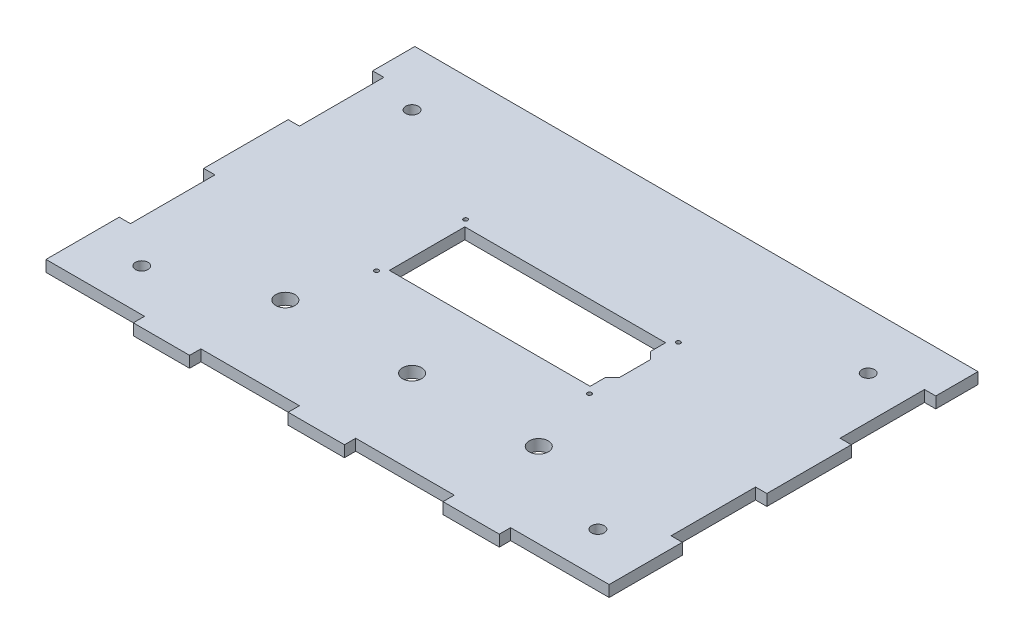
SolidWorks part; units mm, degrees
ref_plane "Plano frontal" through (0, 0, 0) normal (0, 0, 1) x (1, 0, 0)
ref_plane "Plano superior" through (0, 0, 0) normal (0, 1, 0) x (1, 0, 0)
ref_plane "Plano direito" through (0, 0, 0) normal (1, 0, 0) x (0, 0, -1)
sketch "Esboço1" plane through (0, 0, 0) normal (0, 1, 0) x (1, 0, 0)
  line L0 (-100, 75) -> (100, -75) construction
  line L1 (-100, 75) -> (100, 75)
  line L2 (-100, 75) -> (-100, -75)
  line L3 (-100, -75) -> (100, -75)
  line L4 (100, 75) -> (100, -75)
  line L5 (0, 75) -> (0, -75) construction
  line L6 (-100, 0) -> (100, 0) construction
  line L7 (-35.65, -13.4) -> (35.65, -13.4)
  line L8 (-35.65, 13.4) -> (35.65, 13.4)
  line L9 (-35.65, 13.4) -> (-35.65, -13.4)
  line L10 (35.65, 13.4) -> (35.65, 8)
  line L11 (35.65, -13.4) -> (35.65, -8)
  line L12 (35.65, 8) -> (38.15, 5.5)
  line L13 (38.15, 5.5) -> (38.15, -5.5)
  line L14 (38.15, -5.5) -> (35.65, -8)
  circle A0 centre (-37.8, 15.8) radius 0.75
  circle A1 centre (37.8, 15.8) radius 0.75
  circle A2 centre (37.8, -15.8) radius 0.75
  circle A3 centre (-37.8, -15.8) radius 0.75
  point P4 (0, 0)
  point P12 (0, -13.4)
  point P14 (0, 13.4)
  dimension "D3" = 1.5
  dimension "D4" = 37.8
  dimension "D1" = 200
  dimension "D2" = 150
  dimension "D5" = 15.8
  dimension "D8" = 31.6
  dimension "D9" = 75.6
  dimension "D10" = 71.3
  dimension "D11" = 26.8
  dimension "D12" = 13.4
  dimension "D13" = 5.4
  dimension "D14" = 5.4
  dimension "D15" = 2.5
  dimension "D16" = 135
  dimension "D17" = 11
  dimension "D6" = 2
  dimension "D7" = 2
extrude "Ressalto-extrusão1" add sketch "Esboço1" along normal blind 4
sketch "Esboço2" plane through (0, 4, 0) normal (0, 1, 0) x (1, 0, 0)
  line L0 (-65, -75) -> (-65, -71)
  line L1 (-100, -75) -> (100, -75) construction
  line L2 (-65, -71) -> (-45, -71)
  line L3 (-45, -71) -> (-45, -75)
  line L4 (-45, -75) -> (-10, -75)
  line L5 (-10, -75) -> (-10, -71)
  line L6 (-10, -71) -> (10, -71)
  line L7 (10, -71) -> (10, -75)
  line L8 (10, -75) -> (45, -75)
  line L9 (45, -75) -> (45, -71)
  line L10 (45, -71) -> (65, -71)
  line L11 (65, -71) -> (65, -75)
  line L12 (-100, 75) -> (-100, -75) construction
  line L13 (0, 0) -> (0, 75) construction
  line L15 (10, -71) -> (45, -71)
  line L17 (-65, -75) -> (-100, -75)
  line L18 (-100, -75) -> (-100, -71)
  line L19 (-100, -71) -> (-65, -71)
  line L20 (-45, -71) -> (-10, -71)
  line L21 (65, -71) -> (100, -71)
  line L22 (100, -75) -> (100, 75) construction
  line L23 (100, -45) -> (96, -45)
  line L24 (96, -45) -> (96, -15)
  line L25 (96, -15) -> (100, -15)
  line L26 (100, -15) -> (100, 15)
  line L27 (100, 15) -> (96, 15)
  line L28 (96, 15) -> (96, 45)
  line L29 (96, 45) -> (100, 45)
  line L30 (100, 75) -> (-100, 75) construction
  line L31 (-100, -15) -> (-100, -45)
  line L32 (-100, 45) -> (-100, 15)
  line L33 (-96, 45) -> (-100, 45)
  line L34 (100, 45) -> (100, 15)
  line L35 (100, -15) -> (100, -45)
  line L36 (-96, 15) -> (-96, 45)
  line L37 (-100, 15) -> (-96, 15)
  line L38 (-100, -15) -> (-100, 15)
  line L39 (-96, -15) -> (-100, -15)
  line L40 (-96, -45) -> (-96, -15)
  line L41 (-100, -45) -> (-96, -45)
  line M8 (-100, 75) -> (-100, -75)
  line M9 (-100, -75) -> (100, -75)
  line M10 (100, -75) -> (100, 75)
  dimension "D1" = 35
  dimension "D2" = 35
  dimension "D3" = 35
  dimension "D4" = 20
  dimension "D5" = 20
  dimension "D6" = 20
  dimension "D7" = 4
  dimension "D8" = 30
  dimension "D9" = 30
  dimension "D10" = 30
  dimension "D11" = 30
  dimension "D12" = 4
extrude "Corte-extrusão1" cut sketch "Esboço2" against normal through all contours L20 L3 L5 M9 | L15 L7 L9 M9 | L21 L11 M9 M10 | L19 L0 M8 M9 | L27 L28 L29 L34 | L35 L23 L24 L25 | L37 L36 L33 L32 | L31 L41 L40 L39
sketch "Esboço3" plane through (0, 4, 0) normal (0, 1, 0) x (1, 0, 0)
  line L0 (100, 45) -> (100, 75) construction
  line L1 (-100, 75) -> (100, 75)
  line L2 (-100, 75) -> (-100, 60)
  line L3 (-100, 60) -> (100, 60)
  line L4 (100, 75) -> (100, 60)
  dimension "D1" = 15
extrude "Corte-extrusão2" cut sketch "Esboço3" against normal through all
hole_wizard "Furo com folga de M41" positions "3DSketch1" profile "Esboço4" hole size "M4" standard "ISO" end condition through all
sketch3d "3DSketch1"
  line L0 (-100, 4, -60) -> (100, 4, -60) construction
  line L1 (-96, 4, -15) -> (-96, 4, -45) construction
  line L2 (96, 4, -15) -> (96, 4, -45) construction
  line L3 (-100, 4, 71) -> (-65, 4, 71) construction
  line L4 (-96, 4, 45) -> (-96, 4, 15) construction
  line L6 (96, 4, 45) -> (96, 4, 15) construction
  line L7 (65, 4, 71) -> (100, 4, 71) construction
  point P0 (-81, 4, -40)
  point P2 (-81, 4, 56)
  point P4 (81, 4, 56)
  point P6 (81, 4, -40)
  dimension "D1" = 20
  dimension "D2" = 15
  dimension "D3" = 15
  dimension "D4" = 20
  dimension "D5" = 15
  dimension "D6" = 15
  dimension "D7" = 15
  dimension "D8" = 15
sketch "Esboço4" plane through (-81, 4, -40) normal (1, 0, 0) x (0, 0, 1)
  line L0 (0, 0) -> (0, 4)
  line L1 (0, 4) -> (2.25, 4)
  line L2 (2.25, 4) -> (2.25, 0)
  line L5 (2.25, 0) -> (0, 0)
  line L11 (0, -6.35) -> (0, 107.95) construction
  dimension "Thru Hole Dia." = 4.5
  dimension "Thru Hole Depth" = 4
sketch "Esboço5" plane through (0, 4, 0) normal (0, 1, 0) x (1, 0, 0)
  line L0 (0, -13.4) -> (0, -75) construction
  line L3 (-45, -71) -> (-10, -71) construction
  circle A0 centre (-45, -41) radius 3.4
  circle A1 centre (0, -41) radius 3.4
  circle A3 centre (45, -41) radius 3.4
  dimension "D1" = 6.8
  dimension "D2" = 30
  dimension "D3" = 45
extrude "Corte-extrusão3" cut sketch "Esboço5" against normal through all
